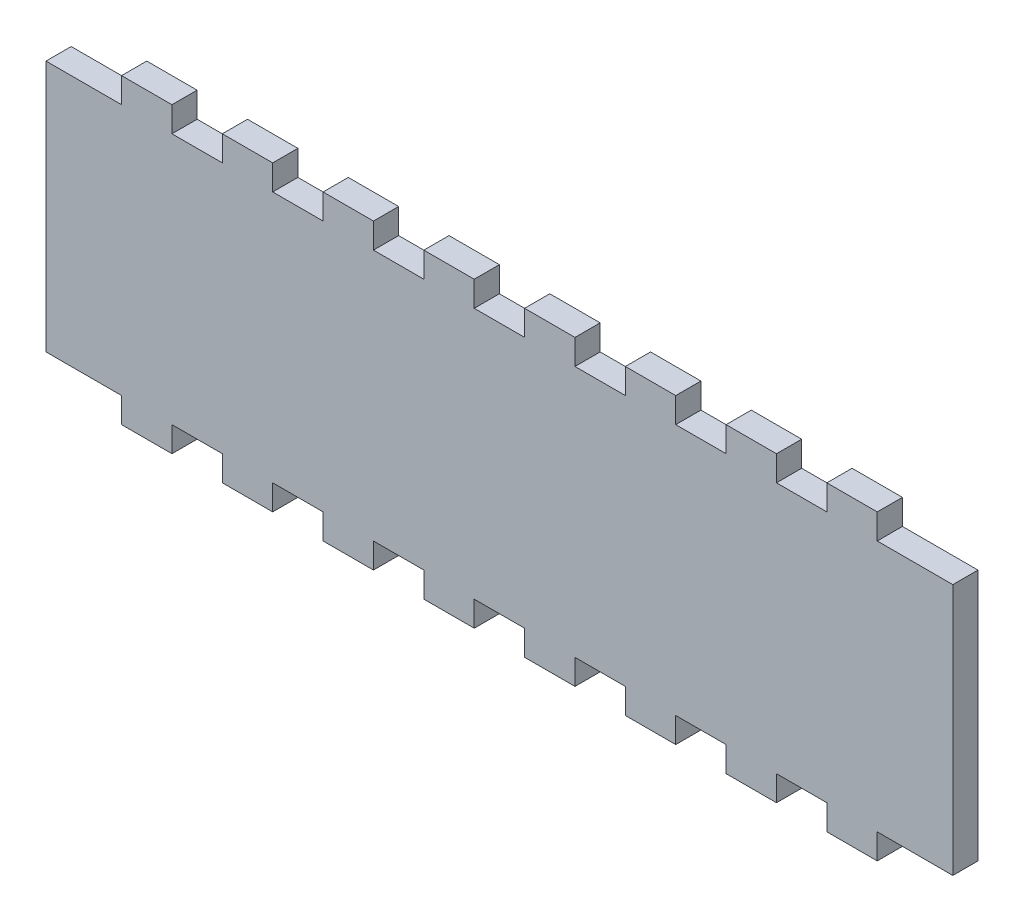
SolidWorks part; units mm, degrees
ref_plane "Front Plane" through (0, 0, 0) normal (0, 0, 1) x (1, 0, 0)
ref_plane "Top Plane" through (0, 0, 0) normal (0, 1, 0) x (1, 0, 0)
ref_plane "Right Plane" through (0, 0, 0) normal (1, 0, 0) x (0, 0, -1)
sketch "Sketch1" plane through (0, 0, 0) normal (0, 0, 1) x (1, 0, 0)
  line L0 (0, 25) -> (180, 25) construction
  line L1 (0, 0) -> (15, 0)
  line L2 (0, 0) -> (0, 50)
  line L3 (0, 50) -> (15, 50)
  line L4 (180, 0) -> (180, 50)
  line L5 (45, 50) -> (55, 50)
  line L6 (15, 50) -> (15, 55)
  line L7 (15, 55) -> (25, 55)
  line L8 (25, 50) -> (25, 55)
  line L9 (165, 50) -> (180, 50)
  line L10 (165, 50) -> (165, 55)
  line L11 (165, 55) -> (155, 55)
  line L12 (155, 50) -> (155, 55)
  line L13 (35, 50) -> (35, 55)
  line L14 (35, 55) -> (45, 55)
  line L15 (45, 50) -> (45, 55)
  line L16 (55, 50) -> (55, 55)
  line L17 (55, 55) -> (65, 55)
  line L18 (65, 50) -> (65, 55)
  line L19 (75, 50) -> (75, 55)
  line L20 (75, 55) -> (85, 55)
  line L21 (85, 50) -> (85, 55)
  line L22 (95, 50) -> (95, 55)
  line L23 (95, 55) -> (105, 55)
  line L24 (105, 50) -> (105, 55)
  line L25 (115, 50) -> (115, 55)
  line L26 (115, 55) -> (125, 55)
  line L27 (125, 50) -> (125, 55)
  line L28 (135, 50) -> (135, 55)
  line L29 (135, 55) -> (145, 55)
  line L30 (145, 50) -> (145, 55)
  line L31 (155, 50) -> (155, 55)
  line L32 (155, 55) -> (165, 55)
  line L33 (165, 50) -> (165, 55)
  line L34 (25, 50) -> (35, 50)
  line L35 (65, 50) -> (75, 50)
  line L36 (85, 50) -> (95, 50)
  line L37 (105, 50) -> (115, 50)
  line L38 (125, 50) -> (135, 50)
  line L39 (145, 50) -> (155, 50)
  line L40 (165, 0) -> (165, -5)
  line L41 (155, 0) -> (155, -5)
  line L42 (145, 0) -> (145, -5)
  line L43 (135, 0) -> (135, -5)
  line L44 (125, 0) -> (125, -5)
  line L45 (115, 0) -> (115, -5)
  line L46 (105, 0) -> (105, -5)
  line L47 (95, 0) -> (95, -5)
  line L48 (85, 0) -> (85, -5)
  line L49 (75, 0) -> (75, -5)
  line L50 (65, 0) -> (65, -5)
  line L51 (55, 0) -> (55, -5)
  line L52 (45, 0) -> (45, -5)
  line L53 (35, 0) -> (35, -5)
  line L54 (25, 0) -> (25, -5)
  line L55 (15, 0) -> (15, -5)
  line L56 (155, -5) -> (165, -5)
  line L57 (135, -5) -> (145, -5)
  line L58 (115, -5) -> (125, -5)
  line L59 (95, -5) -> (105, -5)
  line L60 (75, -5) -> (85, -5)
  line L61 (55, -5) -> (65, -5)
  line L62 (35, -5) -> (45, -5)
  line L63 (165, -5) -> (155, -5)
  line L64 (15, -5) -> (25, -5)
  line L65 (25, 0) -> (35, 0)
  line L66 (45, 0) -> (55, 0)
  line L67 (65, 0) -> (75, 0)
  line L68 (85, 0) -> (95, 0)
  line L69 (105, 0) -> (115, 0)
  line L70 (125, 0) -> (135, 0)
  line L71 (145, 0) -> (155, 0)
  line L72 (165, 0) -> (180, 0)
  line L73 (165, 50) -> (180, 50)
  dimension "D1" = 50
  dimension "D2" = 180
  dimension "D3" = 15
  dimension "D4" = 10
  dimension "D5" = 5
  dimension "D6" = 15
  dimension "D9" = 8
extrude "Boss-Extrude2" add sketch "Sketch1" along normal blind 5 contours L2 L0 L4 L9 L10 L11 L12 L39 L30 L29 L28 L38 L27 L26 L25 L37 L24 L23 L22 L36 L21 L20 L19 L35 L18 L17 L16 L5 L15 L14 L13 L34 L8 L7 L6 L3 | L0 L2 L1 L55 L64 L54 L65 L53 L62 L52 L66 L51 L61 L50 L67 L49 L60 L48 L68 L47 L59 L46 L69 L45 L58 L44 L70 L43 L57 L42 L71 L41 L56 L40 L72 L4
